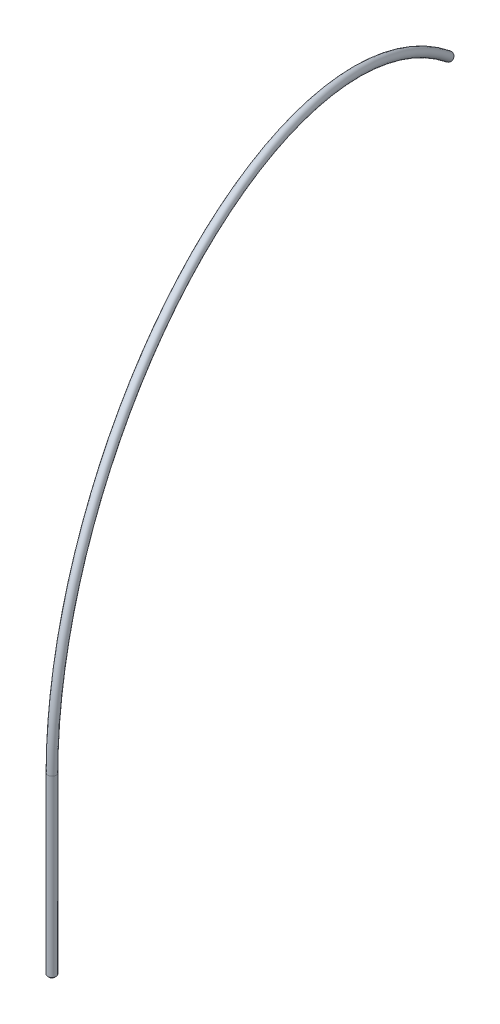
SolidWorks part; units mm, degrees
material "PTFE (general)"
ref_plane "Front Plane" through (0, 0, 0) normal (0, 0, 1) x (1, 0, 0)
ref_plane "Top Plane" through (0, 0, 0) normal (0, 1, 0) x (1, 0, 0)
ref_plane "Right Plane" through (0, 0, 0) normal (1, 0, 0) x (0, 0, -1)
sketch "Sketch1" plane through (0, 0, 0) normal (0, 0, 1) x (1, 0, 0)
  line L0 (0, 0) -> (1.5875, 0) construction
  line L1 (1.5875, 100.7938) -> (2.3812, 100.7938)
  line L2 (1.5875, 100.7938) -> (1.5875, 0)
  line L3 (1.5875, 0) -> (2.3813, 0.7937)
  line L4 (2.3812, 100.7938) -> (2.3813, 0.7937)
  line L5 (0, 0) -> (0, 49.843) construction
  dimension "D1" = 45
  dimension "D2" = 3.175
  dimension "D3" = 4.7625
  dimension "D4" = 100
revolve "Revolve1" add sketch "Sketch1" angle 360 about L5
sketch "Sketch2" plane through (0, 0, 0) normal (0.9631, 0, -0.2692) x (-0.2692, 0, -0.9631)
  line L0 (0, 100.7937) -> (0, 71.387) construction
  line L1 (2.3812, 100.7938) -> (-2.3812, 100.7938) construction
  arc A0 (0, 100.7937) -> (327.7311, 254.6923) centre (200, 100.7938) cw
  dimension "D1" = 200
sketch "Sketch3" plane through (0, 100.7938, 0) normal (0, 1, 0) x (1, 0, 0)
  circle A0 centre (0, 0) radius 1.5875
  circle A1 centre (0, 0) radius 2.3812
  circle A2 centre (0, 0) radius 2.3812 construction
  circle A3 centre (0, 0) radius 1.5875 construction
sweep "Sweep1" add profiles "Sketch3" path "Sketch2"
